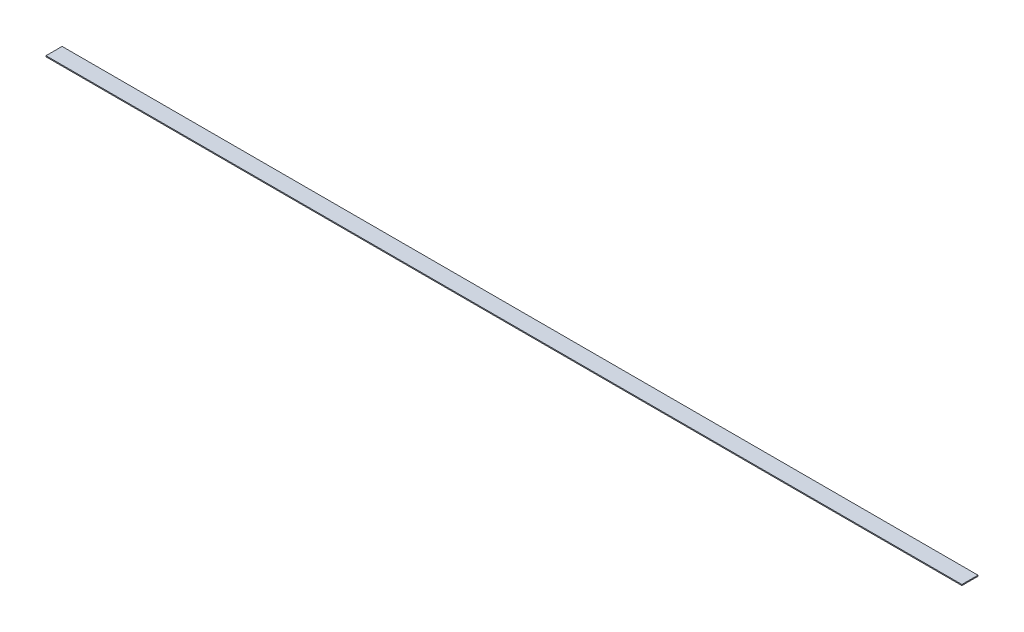
SolidWorks part; units mm, degrees
ref_plane "Front Plane" through (0, 0, 0) normal (0, 0, 1) x (1, 0, 0)
ref_plane "Top Plane" through (0, 0, 0) normal (0, 1, 0) x (1, 0, 0)
ref_plane "Right Plane" through (0, 0, 0) normal (1, 0, 0) x (0, 0, -1)
sketch "Sketch1" plane through (0, 0, 0) normal (0, 1, 0) x (1, 0, 0)
  line L1 (1444.625, 25.4) -> (-1444.625, 25.4)
  line L2 (1444.625, 25.4) -> (1444.625, -25.4)
  line L3 (1444.625, -25.4) -> (-1444.625, -25.4)
  line L4 (-1444.625, 25.4) -> (-1444.625, -25.4)
  line L5 (1444.625, 25.4) -> (-1444.625, -25.4) construction
  line L6 (1444.625, -25.4) -> (-1444.625, 25.4) construction
  point P1 (0, 0)
  dimension "D1" = 50.8
  dimension "D2" = 2889.25
extrude "Boss-Extrude1" add sketch "Sketch1" along normal blind 3.175
